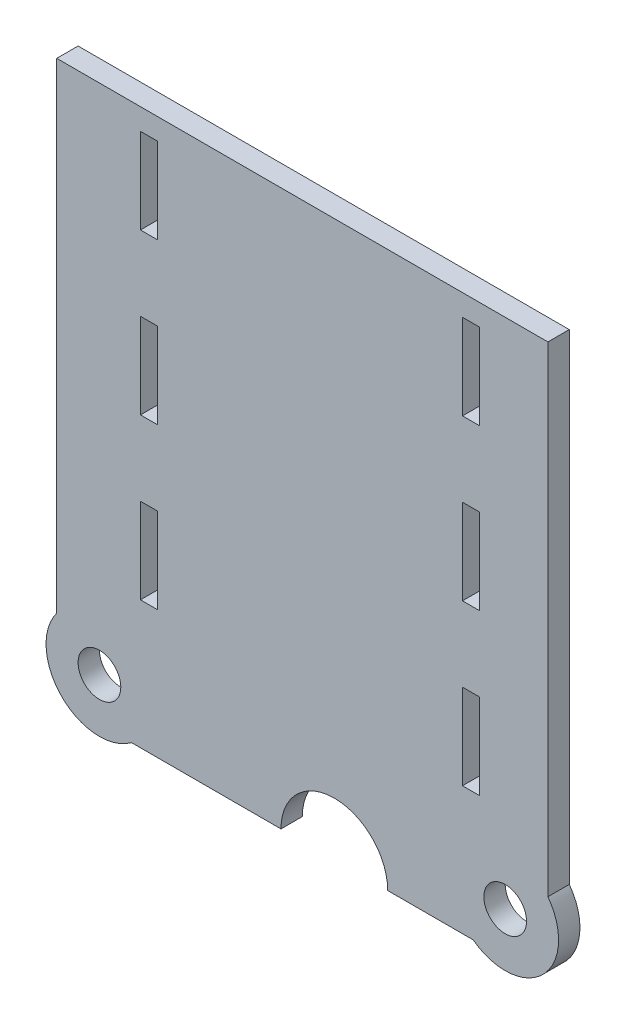
SolidWorks part; units mm, degrees
ref_plane "Front Plane" through (0, 0, 0) normal (0, 0, 1) x (1, 0, 0)
ref_plane "Top Plane" through (0, 0, 0) normal (0, 1, 0) x (1, 0, 0)
ref_plane "Right Plane" through (0, 0, 0) normal (1, 0, 0) x (0, 0, -1)
sketch "Sketch1" plane through (0, 0, 0) normal (0, 0, 1) x (1, 0, 0)
  line L0 (0, 0) -> (0, 152.4) construction
  line L1 (0.0027, -12.7) -> (-50.8, -12.7)
  line L2 (-73.025, 9.525) -> (-73.025, 152.4)
  line L3 (-73.025, 152.4) -> (73.025, 152.4)
  line L4 (73.025, 9.525) -> (73.025, 152.4)
  line L5 (-0.0027, -12.7) -> (50.8, -12.7)
  circle A0 centre (-60.325, 0) radius 6.35
  arc A1 (-73.025, 9.525) -> (-50.8, -12.7) centre (-60.325, 0) ccw
  arc A2 (73.025, 9.525) -> (50.8, -12.7) centre (60.325, 0) cw
  circle A3 centre (60.325, 0) radius 6.35
  dimension "D1" = 12.7
  dimension "D2" = 31.75
  dimension "D3" = 60.325
  dimension "D4" = 146.05
  dimension "D5" = 12.7
  dimension "D6" = 152.4
extrude "Boss-Extrude1" add sketch "Sketch1" along normal mid plane 6.35
sketch "Sketch2" plane through (0, 0, 3.175) normal (0, 0, 1) x (1, 0, 0)
  line L0 (-43.053, 152.4) -> (-43.053, -12.7) construction
  line L1 (-73.025, 152.4) -> (73.025, 152.4) construction
  line L2 (50.8, -12.7) -> (-50.8, -12.7) construction
  line L3 (47.625, 152.4) -> (47.625, -12.7) construction
  line L4 (73.025, 9.525) -> (73.025, 152.4) construction
  line L5 (-73.025, 9.525) -> (-73.025, 152.4) construction
  line L6 (-45.593, 120.65) -> (-45.593, 98.425) construction
  line L7 (-48.133, 146.05) -> (-43.053, 146.05)
  line L8 (-48.133, 146.05) -> (-48.133, 120.65)
  line L9 (-48.133, 120.65) -> (-43.053, 120.65)
  line L10 (-43.053, 146.05) -> (-43.053, 120.65)
  line L11 (-48.133, 98.425) -> (-43.053, 98.425)
  line L12 (-48.133, 98.425) -> (-48.133, 73.025)
  line L13 (-48.133, 73.025) -> (-43.053, 73.025)
  line L14 (-43.053, 98.425) -> (-43.053, 73.025)
  line L15 (-48.133, 50.8) -> (-43.053, 50.8)
  line L16 (-48.133, 50.8) -> (-48.133, 25.4)
  line L17 (-48.133, 25.4) -> (-43.053, 25.4)
  line L18 (-43.053, 50.8) -> (-43.053, 25.4)
  line L19 (-45.593, 73.025) -> (-45.593, 50.8) construction
  line L20 (47.625, 120.65) -> (52.705, 120.65)
  line L21 (52.705, 50.8) -> (52.705, 25.4)
  line L22 (47.625, 146.05) -> (52.705, 146.05)
  line L23 (47.625, 73.025) -> (52.705, 73.025)
  line L24 (47.625, 98.425) -> (47.625, 73.025)
  line L25 (47.625, 98.425) -> (52.705, 98.425)
  line L26 (52.705, 152.4) -> (52.705, -13.9266) construction
  line L27 (47.625, 50.8) -> (47.625, 25.4)
  line L28 (47.625, 25.4) -> (52.705, 25.4)
  line L29 (50.165, 120.65) -> (50.165, 98.425) construction
  line L30 (52.705, 98.425) -> (52.705, 73.025)
  line L31 (52.705, 146.05) -> (52.705, 120.65)
  line L32 (47.625, 146.05) -> (47.625, 120.65)
  line L33 (47.625, 50.8) -> (52.705, 50.8)
  line L34 (50.165, 73.025) -> (50.165, 50.8) construction
  arc A0 (50.8, -12.7) -> (73.025, 9.525) centre (60.325, 0) ccw construction
  dimension "D1" = 25.4
  dimension "D2" = 29.972
  dimension "D3" = 25.4
  dimension "D4" = 5.08
  dimension "D5" = 38.1
  dimension "D6" = 6.35
  dimension "D7" = 5.08
extrude "Cut-Extrude1" cut sketch "Sketch2" against normal through all
sketch "Sketch3" plane through (0, 0, 3.175) normal (0, 0, 1) x (1, 0, 0)
  line L0 (50.8, -12.7) -> (-50.8, -12.7) construction
  line L1 (73.025, 9.525) -> (73.025, 152.4) construction
  circle A0 centre (9.525, -12.7) radius 15.875
  point P4 (8.7709, -12.7)
  dimension "D2" = 31.75
  dimension "D1" = 63.5
extrude "Cut-Extrude2" cut sketch "Sketch3" against normal through all
